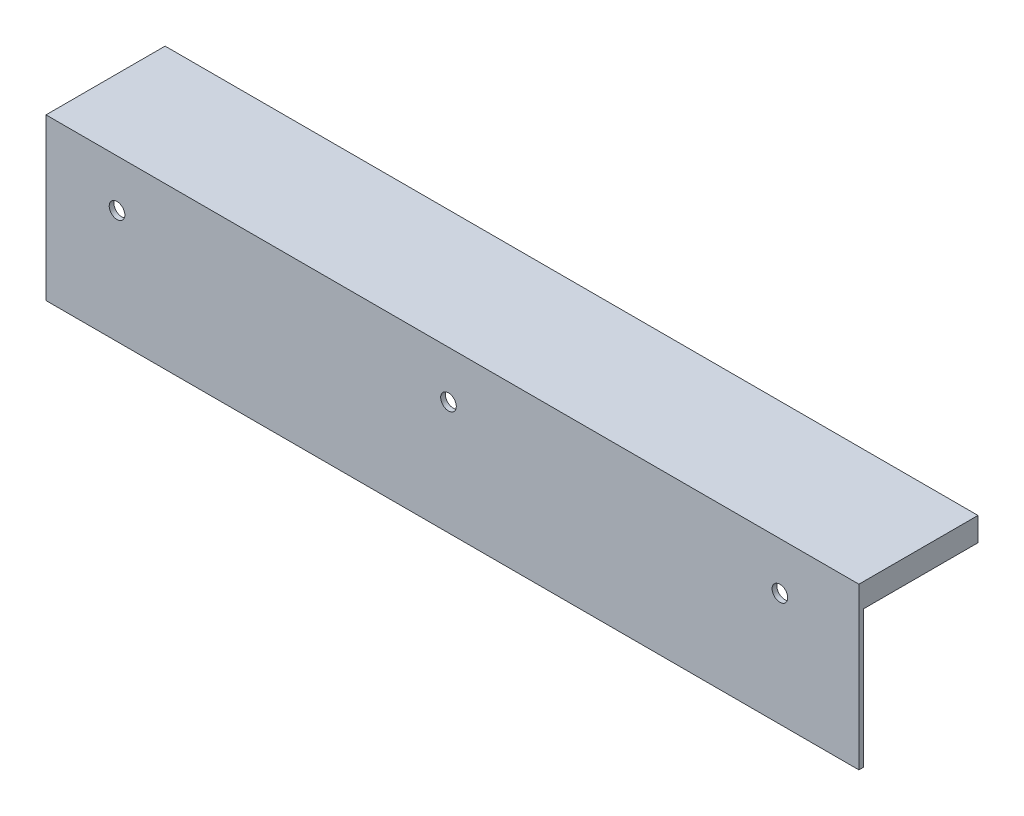
SolidWorks part; units mm, degrees
ref_plane "Front Plane" through (0, 0, 0) normal (0, 0, 1) x (1, 0, 0)
ref_plane "Top Plane" through (0, 0, 0) normal (0, 1, 0) x (1, 0, 0)
ref_plane "Right Plane" through (0, 0, 0) normal (1, 0, 0) x (0, 0, -1)
sketch "Sketch1" plane through (0, 0, 0) normal (0, 0, 1) x (1, 0, 0)
  line L1 (-223.1003, 272.5) -> (-51.4191, 272.5)
  line L2 (-223.1003, 272.5) -> (-223.1003, 243.5306)
  line L3 (-223.1003, 243.5306) -> (-51.4191, 243.5306)
  line L4 (-51.4191, 272.5) -> (-51.4191, 243.5306)
  circle A1 centre (-208.1003, 267.5) radius 1.65
  circle A2 centre (-138.1003, 267.5) radius 1.65
  circle A5 centre (-68.1003, 267.5) radius 1.65
extrude "Boss-Extrude1" add sketch "Sketch1" along normal blind 1
ref_plane "Plane4" through (0, 272.5, 0) normal (0, 1, 0) x (1, 0, 0)
sketch "Sketch7" plane through (0, 272.5, 0) normal (0, 1, 0) x (1, 0, 0)
  line L0 (-223.1003, -1) -> (-51.4191, -1)
  line L1 (-223.1003, -1) -> (-223.1003, 24.1515)
  line L2 (-51.4191, -1) -> (-51.4191, 24.1515)
  line L3 (-223.1003, 24.1515) -> (-51.4191, 24.1515)
extrude "Boss-Extrude2" add sketch "Sketch7" along normal blind 5
